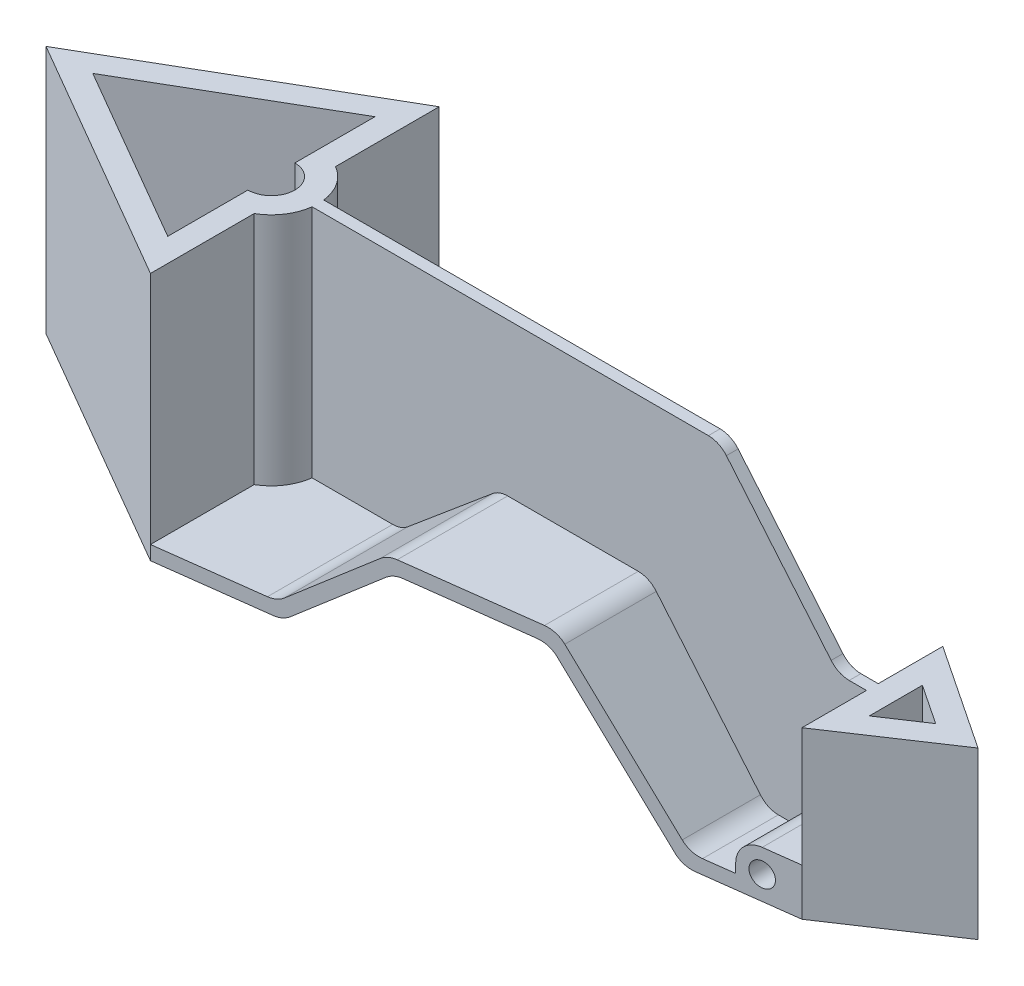
SolidWorks part; units mm, degrees
material "1060 Alloy"
ref_plane "Front Plane" through (0, 0, 0) normal (0, 0, 1) x (1, 0, 0)
ref_plane "Top Plane" through (0, 0, 0) normal (0, 1, 0) x (1, 0, 0)
ref_plane "Right Plane" through (0, 0, 0) normal (1, 0, 0) x (0, 0, -1)
sketch "Sketch2" plane through (0, 0, 0) normal (0, 1, 0) x (1, 0, 0)
  line L0 (0, -61.5) -> (0, 61.5)
  line L1 (0, 61.5) -> (-106, 0)
  line L2 (-106, 0) -> (0, -61.5)
  line L3 (-10, 44.1369) -> (-86.0733, 0)
  line L4 (-86.0733, 0) -> (-10, -44.1369)
  line L5 (-10, -44.1369) -> (-10, 44.1369)
  point P4 (0, 0)
  dimension "D1" = 61.5
  dimension "D2" = 106
  dimension "D3" = 10
extrude "Boss-Extrude1" add sketch "Sketch2" along normal blind 106
sketch "Sketch3" plane through (0, 0, 0) normal (0, 0, 1) x (1, 0, 0)
  line L0 (0, 0) -> (50, 0)
  line L1 (50, 0) -> (91.7114, 35)
  line L2 (91.7114, 35) -> (150.654, 35)
  line L3 (150.654, 35) -> (201, -25)
  line L4 (201, -25) -> (246, -25)
  line L6 (47.8162, 6) -> (89.5276, 41)
  line L7 (89.5276, 41) -> (153.4519, 41)
  line L8 (153.4519, 41) -> (203.7978, -19)
  line L9 (203.7978, -19) -> (221, -19)
  line L10 (0, 6) -> (0, 0)
  line L11 (246, -19) -> (246, -25)
  line L15 (0, 6) -> (47.8162, 6)
  line L16 (0, 6) -> (47.8162, 6) construction
  line L17 (231, -5) -> (246, -5)
  line L18 (246, -5) -> (246, -19)
  line L19 (221, -15) -> (221, -19)
  line L20 (203.7978, -19) -> (246, -19) construction
  circle A2 centre (231, -15) radius 5
  arc A3 (231, -5) -> (221, -15) centre (231, -15) ccw
  point P19 (203, -2.5548)
  dimension "D15" = 10
  dimension "D1" = 50
  dimension "D2" = 35
  dimension "D3" = 60
  dimension "D4" = 45
  dimension "D5" = 140
  dimension "D6" = 130
  dimension "D7" = 246
  dimension "D13" = 6
  dimension "D16" = 10
  dimension "D17" = 15
  dimension "D18" = 10
  dimension "D19" = 20
  dimension "D8" = 6
extrude "Boss-Extrude2" add sketch "Sketch3" along normal mid plane 123
sketch "Sketch4" plane through (0, 0, 0) normal (0, 1, 0) x (1, 0, 0)
  line L0 (246, -30) -> (246, 30)
  line L1 (246, -61.5) -> (246, 61.5) construction
  line L2 (246, 30) -> (291, 0)
  line L3 (291, 0) -> (246, -30)
  line L4 (256, 11.3148) -> (272.9722, 0)
  line L5 (272.9722, 0) -> (256, -11.3148)
  line L6 (256, -11.3148) -> (256, 11.3148)
  point P5 (246, 0)
  dimension "D1" = 30
  dimension "D2" = 45
  dimension "D3" = 10
extrude "Boss-Extrude3" add sketch "Sketch4" along normal blind 70.6667 from surface at -25 starting at face at (223.5, -25, 0)
sketch "Sketch5" plane through (0, 0, 0) normal (0, 0, 1) x (1, 0, 0)
  line L0 (0, 106) -> (183.3267, 106)
  line L1 (183.3267, 106) -> (233.9524, 45.6667)
  line L2 (233.9524, 45.6667) -> (246, 45.6667)
  line L3 (150.654, 35) -> (201, -25) construction
  line L4 (0, 106) -> (0, 6)
  line L5 (246, 45.6667) -> (246, -5) construction
  line L6 (246, -5) -> (231, -5) construction
  line L7 (221, -19) -> (203.7978, -19) construction
  line L8 (203.7978, -19) -> (153.4519, 41) construction
  line L9 (153.4519, 41) -> (89.5276, 41) construction
  line L10 (89.5276, 41) -> (47.8162, 6) construction
  line L11 (47.8162, 6) -> (0, 6) construction
  line L14 (246, 45.6667) -> (246, -5)
  line L15 (246, -5) -> (231, -5)
  line L16 (221, -19) -> (203.7978, -19)
  line L17 (203.7978, -19) -> (153.4519, 41)
  line L18 (153.4519, 41) -> (89.5276, 41)
  line L19 (89.5276, 41) -> (47.8162, 6)
  line L20 (47.8162, 6) -> (0, 6)
  line L23 (221, -15) -> (221, -19) construction
  line L24 (221, -15) -> (221, -19)
  arc A0 (231, -5) -> (221, -15) centre (231, -15) ccw construction
  arc A2 (231, -5) -> (221, -15) centre (231, -15) ccw
  dimension "D1" = 70.6667
extrude "Boss-Extrude4" add sketch "Sketch5" along normal mid plane 5
fillet "Fillet2" radius 10 14 edges at (47.8162, 6, -32) (89.5276, 41, -32) (203.7978, -19, -32) (153.4519, 41, -32) (201, -25, 0) (150.654, 35, 0) (91.7114, 35, 0) (50, 0, 0) (233.9524, 45.6667, 0) (183.3267, 106, 0) (203.7978, -19, 32) (47.8162, 6, 32) (153.4519, 41, 32) (89.5276, 41, 32)
sketch "Sketch6" plane through (0, 0, 0) normal (0, 1, 0) x (1, 0, 0)
  line L0 (0, 61.5) -> (246, 61.5)
  line L1 (246, 61.5) -> (246, 30)
  line L2 (246, 30) -> (0, 61.5)
  line L3 (0, -61.5) -> (246, -30)
  line L4 (246, -30) -> (246, -61.5)
  line L5 (246, -61.5) -> (0, -61.5)
extrude "Cut-Extrude1" cut sketch "Sketch6" against normal through all both and the other way through all
sketch "Sketch7" plane through (0, 0, 0) normal (0, 1, 0) x (1, 0, 0)
  line L0 (-106, 0) -> (0, 0) construction
  line L1 (-10, -44.1369) -> (-10, 44.1369) construction
  circle A0 centre (-10, 0) radius 20
  circle A1 centre (-10, 0) radius 10
  point P4 (-10, 0)
  dimension "D1" = 40
  dimension "D3" = 20
  dimension "D2" = 10
extrude "Boss-Extrude5" add sketch "Sketch7" along normal up to surface (106 mm away) up to face at (35.9039, 106, 0)
sketch "Sketch8" plane through (0, 106, 0) normal (0, 1, 0) x (1, 0, 0)
  line L0 (-10, -10) -> (-10, 10) construction
  line L1 (-86.0733, 0) -> (-10, 44.1369)
  line L2 (-10, 44.1369) -> (-10, 10)
  line L3 (-86.0733, 0) -> (-10, -44.1369)
  line L4 (-10, -44.1369) -> (-10, -10)
  arc A0 (-10, -10) -> (-10, 10) centre (-10, 0) ccw
extrude "Cut-Extrude2" cut sketch "Sketch8" against normal through all both and the other way through all
equation "\"A\" = 246"
equation "\"B\"= 106"
equation "\"D1@Sketch2\"=\"A\"/4"
equation "\"D2@Sketch2\"=\"B\""
equation "\"D1@Boss-Extrude1\"=\"B\""
equation "\"D7@Sketch3\"=\"A\""
equation "\"D1@Boss-Extrude2\"=\"A\"/2"
equation "\"D1@Boss-Extrude3\"=\"B\"*2/3"
equation "\"D1@Boss-Extrude4\"=\"A\"/2"
equation "\"Z\"= ( \"A\" / 8 ) - 5"
equation "\"X\"= \"A\" / 4"
equation "\"Y\"= ( 2 * \"B\" ) / 3"
equation "\"D1@Sketch5\"=\"Y\""
